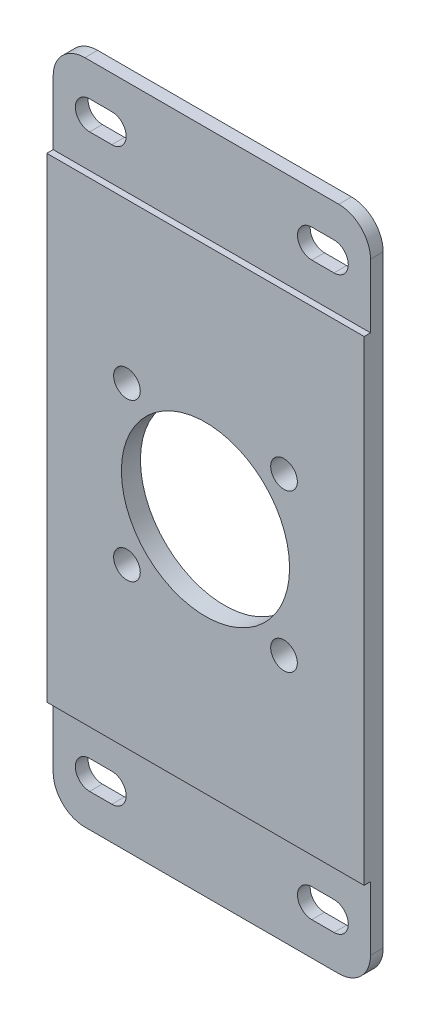
SolidWorks part; units mm, degrees
material "3.1325 (EN-AW 2017A)"
ref_plane "正面" through (0, 0, 0) normal (0, 0, 1) x (1, 0, 0)
ref_plane "平面" through (0, 0, 0) normal (0, 1, 0) x (1, 0, 0)
ref_plane "右側面" through (0, 0, 0) normal (1, 0, 0) x (0, 0, -1)
sketch "ｽｹｯﾁ2" plane through (0, 0, 0) normal (0, 0, 1) x (1, 0, 0)
  line L0 (25, 105) -> (25, 0) construction
  line L1 (0, 0) -> (50, 0)
  line L2 (0, 0) -> (0, 105)
  line L3 (0, 105) -> (50, 105)
  line L4 (50, 0) -> (50, 105)
  line L5 (7.5, 97.5) -> (42.5, 97.5) construction
  line L6 (7.5, 7.5) -> (42.5, 7.5) construction
  line L7 (12.6256, 40.1256) -> (37.3744, 64.8744) construction
  line L8 (37.3744, 40.1256) -> (12.6256, 64.8744) construction
  line L9 (5.75, 7.5) -> (9.25, 7.5) construction
  line L10 (5.75, 9.75) -> (9.25, 9.75)
  line L11 (5.75, 5.25) -> (9.25, 5.25)
  line L12 (40.75, 7.5) -> (44.25, 7.5) construction
  line L13 (40.75, 9.75) -> (44.25, 9.75)
  line L14 (40.75, 5.25) -> (44.25, 5.25)
  line L15 (40.75, 97.5) -> (44.25, 97.5) construction
  line L16 (40.75, 99.75) -> (44.25, 99.75)
  line L17 (40.75, 95.25) -> (44.25, 95.25)
  line L18 (5.75, 97.5) -> (9.25, 97.5) construction
  line L19 (5.75, 99.75) -> (9.25, 99.75)
  line L20 (5.75, 95.25) -> (9.25, 95.25)
  circle A0 centre (25, 52.5) radius 13.25
  circle A10 centre (37.3744, 64.8744) radius 2.1
  circle A11 centre (12.6256, 64.8744) radius 2.1
  circle A12 centre (37.3744, 40.1256) radius 2.1
  circle A13 centre (12.6256, 40.1256) radius 2.1
  arc A14 (5.75, 9.75) -> (5.75, 5.25) centre (5.75, 7.5) ccw
  arc A15 (9.25, 5.25) -> (9.25, 9.75) centre (9.25, 7.5) ccw
  arc A16 (40.75, 9.75) -> (40.75, 5.25) centre (40.75, 7.5) ccw
  arc A17 (44.25, 5.25) -> (44.25, 9.75) centre (44.25, 7.5) ccw
  arc A18 (40.75, 99.75) -> (40.75, 95.25) centre (40.75, 97.5) ccw
  arc A19 (44.25, 95.25) -> (44.25, 99.75) centre (44.25, 97.5) ccw
  arc A20 (5.75, 99.75) -> (5.75, 95.25) centre (5.75, 97.5) ccw
  arc A21 (9.25, 95.25) -> (9.25, 99.75) centre (9.25, 97.5) ccw
  point P13 (25, 52.5)
  point P16 (25, 52.5)
  point P21 (25, 97.5)
  point P24 (25, 7.5)
  point P31 (7.5, 7.5)
  point P36 (42.5, 7.5)
  point P43 (42.5, 97.5)
  point P50 (7.5, 97.5)
  dimension "D2" = 26.5
  dimension "D3" = 35
  dimension "D4" = 45
  dimension "D6" = 7.5
  dimension "D8" = 35
  dimension "D9" = 2
  dimension "D10" = 4.2
  dimension "D12" = 2.25
  dimension "D1" = 90
  dimension "D5" = 50
  dimension "D7" = 7.5
  dimension "D11" = 3.5
  dimension "D13" = 2
extrude "ﾎﾞｽ - 押し出し1" add sketch "ｽｹｯﾁ2" along normal blind 3
sketch "ｽｹｯﾁ3" plane through (0, 0, 3) normal (0, 0, 1) x (1, 0, 0)
  line L0 (50, 0) -> (50, 105) construction
  line L1 (0, 105) -> (50, 105)
  line L2 (0, 105) -> (0, 89.95)
  line L3 (0, 89.95) -> (50, 89.95)
  line L4 (50, 105) -> (50, 89.95)
  line L6 (0, 0) -> (50, 0)
  line L7 (0, 0) -> (0, 15.05)
  line L8 (0, 15.05) -> (50, 15.05)
  line L9 (50, 0) -> (50, 15.05)
  dimension "D1" = 15.05
  dimension "D2" = 15.05
extrude "ｶｯﾄ - 押し出し1" cut sketch "ｽｹｯﾁ3" against normal blind 1
fillet "ﾌｨﾚｯﾄ1" radius 5 4 edges at (0, 0, 1) (50, 0, 1) (0, 105, 1) (50, 105, 1)
